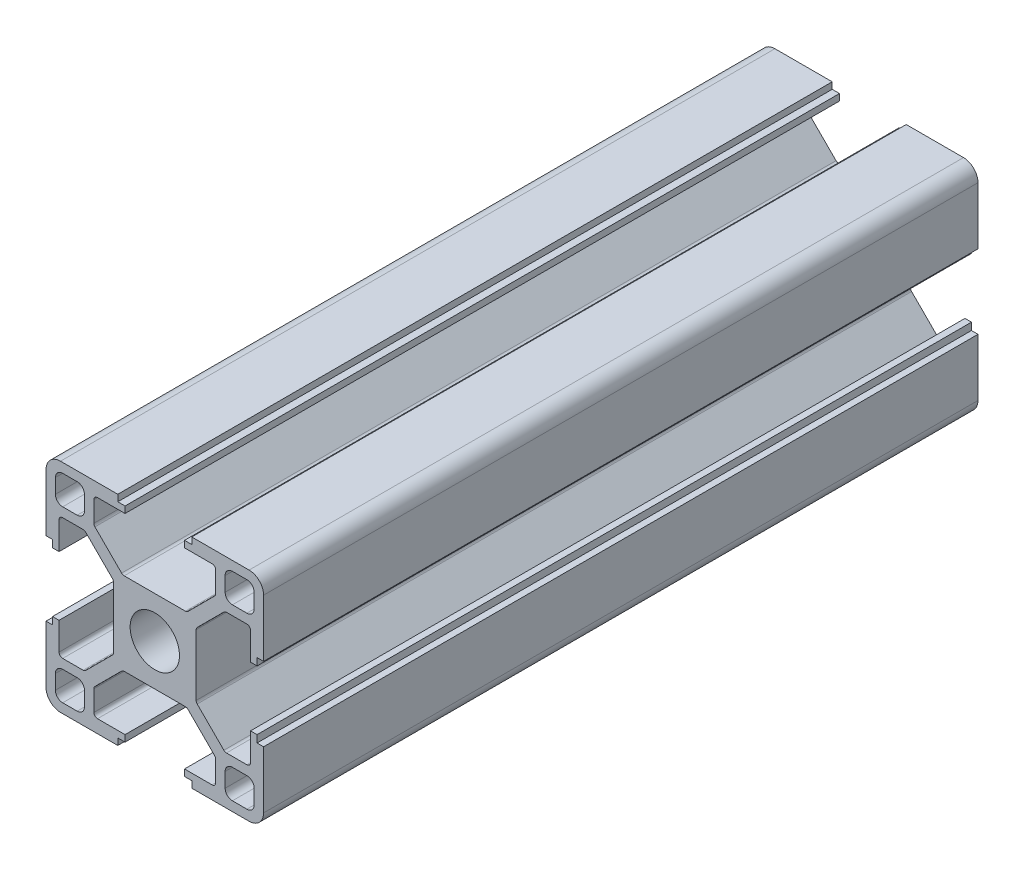
SolidWorks part; units mm, degrees
ref_plane "前视基准面" through (0, 0, 0) normal (0, 0, 1) x (1, 0, 0)
ref_plane "上视基准面" through (0, 0, 0) normal (0, 1, 0) x (1, 0, 0)
ref_plane "右视基准面" through (0, 0, 0) normal (1, 0, 0) x (0, 0, -1)
sketch "草图1" plane through (0, 0, 0) normal (0, 0, 1) x (1, 0, 0)
  line L0 (0, 0) -> (0, 65.3905) construction
  line L1 (0, 0) -> (64.2648, 0) construction
  line L2 (0, 0) -> (79.9729, 79.9729) construction
  line L3 (5.7, 0) -> (5.7, 4.4272)
  line L4 (5.7, 4.4272) -> (9.6728, 8.4)
  line L5 (9.6728, 8.4) -> (13.2, 8.4)
  line L6 (13.2, 8.4) -> (13.2, 4.1)
  line L7 (13.2, 4.1) -> (14.1, 4.1)
  line L8 (14.1, 4.1) -> (14.1, 5.1)
  line L9 (14.1, 5.1) -> (15, 5.1)
  line L10 (15, 5.1) -> (15, 15)
  line L11 (5.1, 15) -> (15, 15)
  line L12 (5.1, 14.1) -> (5.1, 15)
  line L13 (4.1, 14.1) -> (5.1, 14.1)
  line L14 (4.1, 13.2) -> (4.1, 14.1)
  line L15 (8.4, 13.2) -> (4.1, 13.2)
  line L16 (8.4, 9.6728) -> (8.4, 13.2)
  line L17 (4.4272, 5.7) -> (8.4, 9.6728)
  line L18 (0, 5.7) -> (4.4272, 5.7)
  line L20 (9.7, 9.7) -> (13.7, 9.7)
  line L21 (9.7, 9.7) -> (9.7, 13.7)
  line L22 (9.7, 13.7) -> (13.7, 13.7)
  line L23 (13.7, 9.7) -> (13.7, 13.7)
  line L24 (9.7, 9.7) -> (13.7, 13.7) construction
  line L25 (9.7, 13.7) -> (13.7, 9.7) construction
  line L26 (0, 5.7) -> (0, 0)
  line L27 (0, 0) -> (5.7, 0)
  point P9 (11.7, 11.7)
  dimension "D1" = 45
  dimension "D2" = 5.7
  dimension "D3" = 1.8
  dimension "D4" = 0.9
  dimension "D5" = 8.2
  dimension "D6" = 10.2
  dimension "D7" = 1.8
  dimension "D8" = 15
  dimension "D9" = 16.8
  dimension "D10" = 4
  dimension "D11" = 1.3
extrude "凸台-拉伸1" add sketch "草图1" along normal blind 98.5 contours L3 L4 L5 L6 L7 L8 L9 L10 L11 L12 L13 L14 L15 L16 L17 L18 L26 L27
fillet "圆角1" radius 1 4 edges at (9.7, 9.7, 49.25) (13.7, 9.7, 49.25) (9.7, 13.7, 49.25) (13.7, 13.7, 49.25)
fillet "圆角2" radius 2 1 edges at (15, 15, 49.25)
fillet "圆角3" radius 0.5 6 edges at (5.7, 4.4272, 49.25) (4.4272, 5.7, 49.25) (8.4, 13.2, 49.25) (8.4, 9.6728, 49.25) (9.6728, 8.4, 49.25) (13.2, 8.4, 49.25)
pattern_circular "阵列(圆周)1" count 4 over 360 about axis through (0, 0, 0) along (0, 0, 1) of "圆角2", "圆角3", "凸台-拉伸1", "圆角1"
sketch "草图2" plane through (0, 0, 98.5) normal (0, 0, 1) x (1, 0, 0)
  circle A0 centre (0, 0) radius 3.4
  dimension "D1" = 6.8
extrude "切除-拉伸1" cut sketch "草图2" against normal through all
